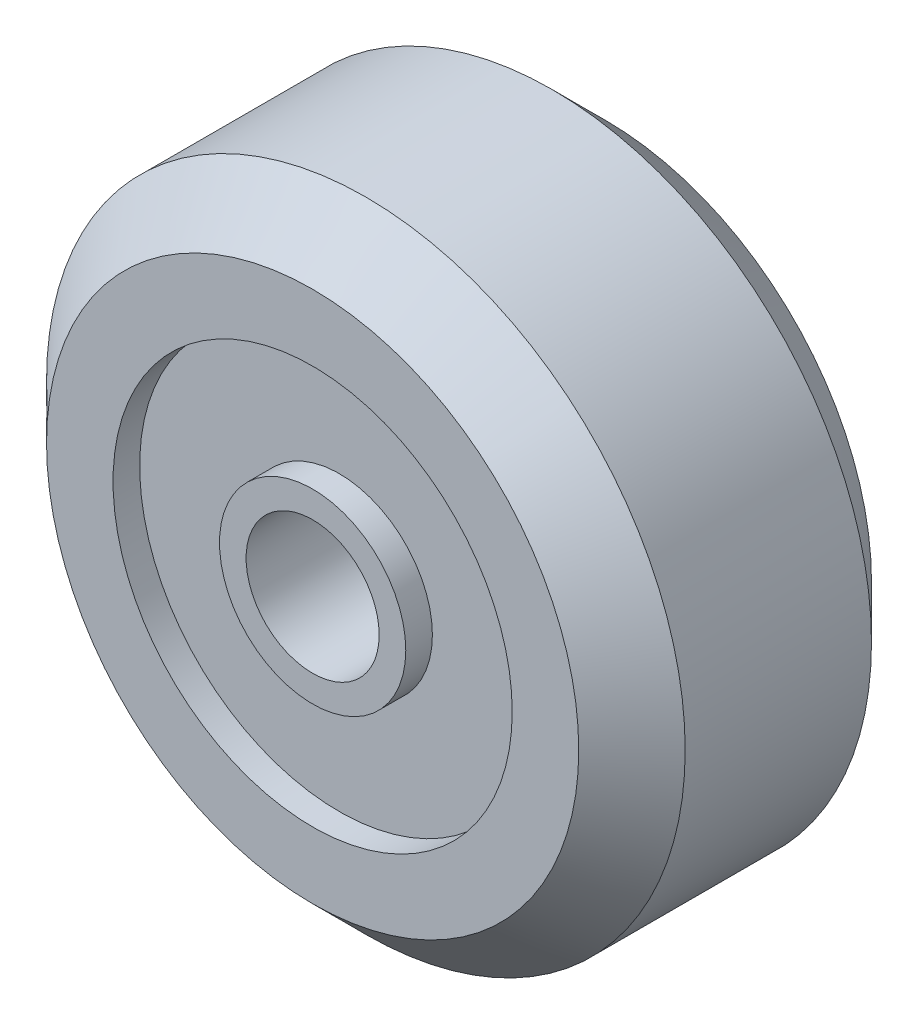
SolidWorks part; units mm, degrees
ref_plane "Front Plane" through (0, 0, 0) normal (0, 0, 1) x (1, 0, 0)
ref_plane "Top Plane" through (0, 0, 0) normal (0, 1, 0) x (1, 0, 0)
ref_plane "Right Plane" through (0, 0, 0) normal (1, 0, 0) x (0, 0, -1)
sketch "Sketch1" plane through (0, 0, 0) normal (0, 0, 1) x (1, 0, 0)
  circle A0 centre (0, 0) radius 12
  dimension "D1" = 24
extrude "Boss-Extrude1" add sketch "Sketch1" along normal blind 11
chamfer "Chamfer1" distance 2 angle 45 2 edges at (12, 0, 0) (12, 0, 11)
sketch "Sketch2" plane through (0, 0, 11) normal (0, 0, 1) x (1, 0, 0)
  circle A0 centre (0, 0) radius 2.5
  dimension "D1" = 5
extrude "Cut-Extrude1" cut sketch "Sketch2" against normal through all
sketch "Sketch3" plane through (0, 0, 11) normal (0, 0, 1) x (1, 0, 0)
  circle A1 centre (0, 0) radius 7.5
  circle A2 centre (0, 0) radius 3.5
  circle A3 centre (0, 0) radius 3.5
  dimension "D1" = 1
  dimension "D2" = 4
extrude "Cut-Extrude2" cut sketch "Sketch3" against normal blind 1
sketch "Sketch4" plane through (0, 0, 0) normal (0, 0, -1) x (-1, 0, 0)
  circle A1 centre (0, 0) radius 7.5
  circle A2 centre (0, 0) radius 3.5
  circle A3 centre (0, 0) radius 3.5
  dimension "D1" = 1
  dimension "D2" = 4
extrude "Cut-Extrude3" cut sketch "Sketch4" against normal blind 1
